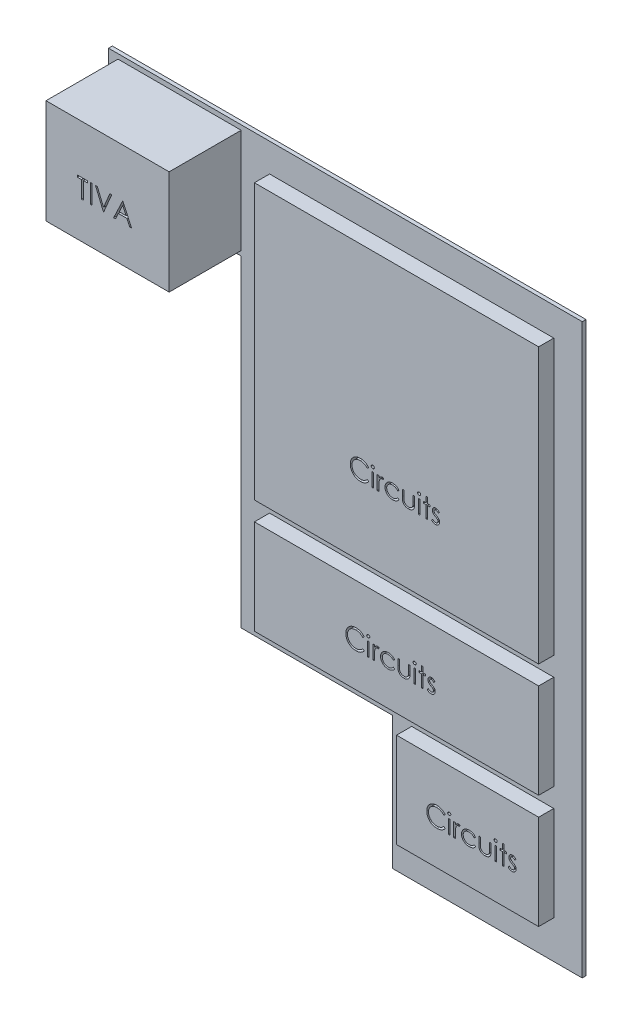
SolidWorks part; units mm, degrees
ref_plane "Front Plane" through (0, 0, 0) normal (0, 0, 1) x (1, 0, 0)
ref_plane "Top Plane" through (0, 0, 0) normal (0, 1, 0) x (1, 0, 0)
ref_plane "Right Plane" through (0, 0, 0) normal (1, 0, 0) x (0, 0, -1)
sketch "Sketch1" plane through (0, 0, 0) normal (0, 0, 1) x (1, 0, 0)
  line L0 (0, 381) -> (-88.9, 381)
  line L1 (0, 0) -> (228.6, 0)
  line L2 (0, 0) -> (0, 304.8)
  line L3 (0, 381) -> (228.6, 381)
  line L4 (228.6, 0) -> (228.6, 381)
  line L5 (-88.9, 381) -> (-88.9, 304.8)
  line L6 (-88.9, 304.8) -> (0, 304.8)
  point P8 (0, 304.8)
  point P9 (0, 301.9217)
  point P10 (-88.9, 304.8)
  point P11 (-88.9, 381)
  point P12 (225.5233, 380.9876)
  point P13 (0, 0)
  dimension "D1" = 228.6
  dimension "D2" = 381
  dimension "D3" = 76.2
  dimension "D4" = 88.9
extrude "Boss-Extrude1" add sketch "Sketch1" along normal blind 2.54 contours L0 L5 L6 L2 L1 L4 L3
sketch "Sketch2" plane through (0, 0, 2.54) normal (0, 0, 1) x (1, 0, 0)
  line L0 (-82.55, 342.9) -> (-88.9, 342.9) construction
  line L1 (-82.55, 377.825) -> (0, 377.825)
  line L2 (-82.55, 377.825) -> (-82.55, 307.975)
  line L3 (-82.55, 307.975) -> (0, 307.975)
  line L4 (0, 377.825) -> (0, 307.975)
  line L5 (-88.9, 381) -> (-88.9, 304.8) construction
  point P8 (-88.9, 342.9)
  dimension "D1" = 82.55
  dimension "D2" = 69.85
  dimension "D3" = 6.35
extrude "Boss-Extrude2" add sketch "Sketch2" along normal blind 48.26
sketch "Sketch3" plane through (0, 0, 2.54) normal (0, 0, 1) x (1, 0, 0)
  line L0 (228.6, 0) -> (228.6, 381) construction
  line L1 (19.05, 361.95) -> (209.55, 361.95)
  line L2 (19.05, 361.95) -> (19.05, 177.8)
  line L3 (19.05, 177.8) -> (209.55, 177.8)
  line L4 (209.55, 361.95) -> (209.55, 177.8)
  line L5 (19.05, 165.1) -> (209.55, 165.1)
  line L6 (19.05, 165.1) -> (19.05, 101.6)
  line L7 (19.05, 101.6) -> (209.55, 101.6)
  line L8 (209.55, 165.1) -> (209.55, 101.6)
  line L9 (209.55, 88.9) -> (114.3, 88.9)
  line L10 (209.55, 88.9) -> (209.55, 25.4)
  line L11 (209.55, 25.4) -> (114.3, 25.4)
  line L12 (114.3, 88.9) -> (114.3, 25.4)
  line L13 (0, 0) -> (0, 304.8) construction
  line L14 (-88.9, 381) -> (228.6, 381) construction
  line L15 (0, 0) -> (228.6, 0) construction
  point P12 (114.3, 101.6)
  point P13 (75.8839, 114.6888)
  point P14 (192.084, 171.9973)
  dimension "D1" = 19.05
  dimension "D2" = 19.05
  dimension "D3" = 19.05
  dimension "D4" = 12.7
  dimension "D5" = 12.7
  dimension "D6" = 25.4
  dimension "D7" = 63.5
extrude "Boss-Extrude3" add sketch "Sketch3" along normal blind 10.16
sketch "Sketch4" plane through (0, 0, 50.8) normal (0, 0, 1) x (1, 0, 0)
  text T0 "TIVA" font "Century Gothic" height 12.7
extrude "Tiva" cut sketch "Sketch4" against normal blind 5.08
sketch "Sketch5" plane through (0, 0, 12.7) normal (0, 0, 1) x (1, 0, 0)
  text T1 "Circuits" font "Century Gothic" height 12.7
extrude "Cut-Extrude2" cut sketch "Sketch5" against normal blind 5.08
sketch "Sketch6" plane through (0, 0, 12.7) normal (0, 0, 1) x (1, 0, 0)
  text T1 "Circuits" font "Century Gothic" height 12.7
extrude "Cut-Extrude3" cut sketch "Sketch6" against normal blind 5.08
sketch "Sketch7" plane through (0, 0, 12.7) normal (0, 0, 1) x (1, 0, 0)
  text T1 "Circuits" font "Century Gothic" height 12.7
extrude "Cut-Extrude4" cut sketch "Sketch7" against normal blind 5.08
sketch "Sketch8" plane through (0, 0, 2.54) normal (0, 0, 1) x (1, 0, 0)
  line L0 (209.55, 88.9) -> (114.3, 88.9) construction
  line L1 (0, 0) -> (101.6, 0)
  line L2 (0, 0) -> (0, 88.9)
  line L3 (0, 88.9) -> (101.6, 88.9)
  line L4 (101.6, 0) -> (101.6, 88.9)
  line L5 (114.3, 88.9) -> (114.3, 25.4) construction
  dimension "D1" = 12.7
extrude "Cut-Extrude5" cut sketch "Sketch8" against normal through all
